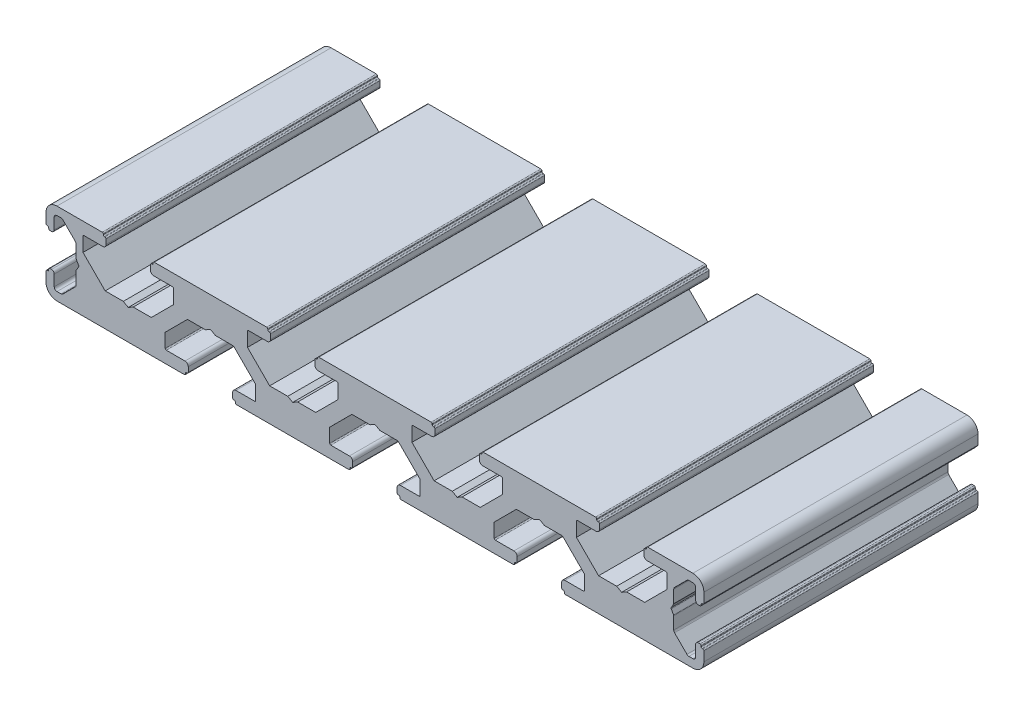
SolidWorks part; units mm, degrees
ref_plane "Płaszczyzna przednia" through (0, 0, 0) normal (0, 0, 1) x (1, 0, 0)
ref_plane "Płaszczyzna górna" through (0, 0, 0) normal (0, 1, 0) x (1, 0, 0)
ref_plane "Płaszczyzna prawa" through (0, 0, 0) normal (1, 0, 0) x (0, 0, -1)
sketch "Szkic1" plane through (0, 0, 0) normal (0, 0, 1) x (1, 0, 0)
  line L0 (141.56, 44.5751) -> (142.46, 44.06)
  line L1 (142.46, 44.06) -> (145.7645, 44.06)
  line L2 (145.7645, 44.06) -> (149.81, 40.01)
  line L3 (149.81, 40.01) -> (149.81, 37.46)
  line L4 (149.61, 37.26) -> (146.21, 37.26)
  line L5 (145.61, 36.66) -> (145.61, 35.76)
  line L6 (145.81, 35.56) -> (145.91, 35.56)
  line L7 (146.11, 35.36) -> (146.11, 35.26)
  line L8 (83.56, 50.06) -> (91.81, 50.06)
  line L9 (83.56, 35.06) -> (106.81, 35.06)
  line L10 (131.11, 49.86) -> (131.11, 49.76)
  line L11 (130.91, 49.56) -> (130.81, 49.56)
  line L12 (130.61, 49.36) -> (130.61, 48.46)
  line L13 (131.21, 47.86) -> (134.61, 47.86)
  line L14 (134.81, 47.66) -> (134.81, 45.11)
  line L15 (134.81, 45.11) -> (130.7645, 41.06)
  line L16 (130.7645, 41.06) -> (127.46, 41.06)
  line L17 (127.46, 41.06) -> (126.56, 40.5449)
  line L18 (126.56, 40.5449) -> (125.66, 41.06)
  line L19 (125.66, 41.06) -> (122.3555, 41.06)
  line L20 (122.3555, 41.06) -> (118.31, 45.11)
  line L21 (118.31, 45.11) -> (118.31, 47.66)
  line L22 (118.51, 47.86) -> (121.91, 47.86)
  line L23 (122.51, 48.46) -> (122.51, 49.36)
  line L24 (111.56, 44.5751) -> (112.46, 44.06)
  line L25 (112.46, 44.06) -> (115.7645, 44.06)
  line L26 (115.7645, 44.06) -> (119.81, 40.01)
  line L27 (119.81, 40.01) -> (119.81, 37.46)
  line L28 (119.61, 37.26) -> (116.21, 37.26)
  line L29 (115.61, 36.66) -> (115.61, 35.76)
  line L30 (115.81, 35.56) -> (115.91, 35.56)
  line L31 (116.11, 35.36) -> (116.11, 35.26)
  line L32 (101.31, 50.06) -> (121.81, 50.06)
  line L33 (122.31, 49.56) -> (122.21, 49.56)
  line L34 (122.01, 49.76) -> (122.01, 49.86)
  line L35 (116.31, 35.06) -> (136.81, 35.06)
  line L36 (131.31, 50.06) -> (151.81, 50.06)
  line L37 (137.01, 35.26) -> (137.01, 35.36)
  line L38 (137.21, 35.56) -> (137.31, 35.56)
  line L39 (137.51, 35.76) -> (137.51, 36.66)
  line L40 (136.91, 37.26) -> (133.51, 37.26)
  line L41 (133.31, 37.46) -> (133.31, 40.01)
  line L42 (133.31, 40.01) -> (137.3555, 44.06)
  line L43 (137.3555, 44.06) -> (140.66, 44.06)
  line L44 (140.66, 44.06) -> (141.56, 44.5751)
  line L45 (171.56, 44.5751) -> (172.46, 44.06)
  line L46 (172.46, 44.06) -> (175.7645, 44.06)
  line L47 (175.7645, 44.06) -> (179.81, 40.01)
  line L48 (179.81, 40.01) -> (179.81, 37.46)
  line L49 (179.61, 37.26) -> (176.21, 37.26)
  line L50 (175.61, 36.66) -> (175.61, 35.76)
  line L51 (146.31, 35.06) -> (166.81, 35.06)
  line L52 (101.11, 49.86) -> (101.11, 49.76)
  line L53 (100.91, 49.56) -> (100.81, 49.56)
  line L54 (100.61, 49.36) -> (100.61, 48.46)
  line L55 (101.21, 47.86) -> (104.61, 47.86)
  line L56 (104.81, 47.66) -> (104.81, 45.11)
  line L57 (104.81, 45.11) -> (100.7645, 41.06)
  line L58 (100.7645, 41.06) -> (97.46, 41.06)
  line L59 (97.46, 41.06) -> (96.56, 40.5449)
  line L60 (96.56, 40.5449) -> (95.66, 41.06)
  line L61 (95.66, 41.06) -> (92.3555, 41.06)
  line L62 (92.3555, 41.06) -> (88.31, 45.11)
  line L63 (88.31, 45.11) -> (88.31, 47.66)
  line L64 (88.51, 47.86) -> (91.91, 47.86)
  line L65 (92.51, 48.46) -> (92.51, 49.36)
  line L66 (92.31, 49.56) -> (92.21, 49.56)
  line L67 (92.01, 49.76) -> (92.01, 49.86)
  line L68 (161.31, 50.06) -> (181.81, 50.06)
  line L69 (175.81, 35.56) -> (175.91, 35.56)
  line L70 (176.11, 35.36) -> (176.11, 35.26)
  line L71 (176.31, 35.06) -> (199.56, 35.06)
  line L72 (191.31, 50.06) -> (199.56, 50.06)
  line L73 (161.11, 49.86) -> (161.11, 49.76)
  line L74 (160.91, 49.56) -> (160.81, 49.56)
  line L75 (160.61, 49.36) -> (160.61, 48.46)
  line L76 (161.21, 47.86) -> (164.61, 47.86)
  line L77 (164.81, 47.66) -> (164.81, 45.11)
  line L78 (164.81, 45.11) -> (160.7645, 41.06)
  line L79 (160.7645, 41.06) -> (157.46, 41.06)
  line L80 (157.46, 41.06) -> (156.56, 40.5449)
  line L81 (156.56, 40.5449) -> (155.66, 41.06)
  line L82 (155.66, 41.06) -> (152.3555, 41.06)
  line L83 (152.3555, 41.06) -> (148.31, 45.11)
  line L84 (148.31, 45.11) -> (148.31, 47.66)
  line L85 (148.51, 47.86) -> (151.91, 47.86)
  line L86 (152.51, 48.46) -> (152.51, 49.36)
  line L88 (107.01, 35.26) -> (107.01, 35.36)
  line L89 (107.21, 35.56) -> (107.31, 35.56)
  line L90 (107.51, 35.76) -> (107.51, 36.66)
  line L91 (106.91, 37.26) -> (103.51, 37.26)
  line L92 (103.31, 37.46) -> (103.31, 40.01)
  line L93 (103.31, 40.01) -> (107.3555, 44.06)
  line L94 (107.3555, 44.06) -> (110.66, 44.06)
  line L95 (110.66, 44.06) -> (111.56, 44.5751)
  line L96 (152.31, 49.56) -> (152.21, 49.56)
  line L97 (152.01, 49.76) -> (152.01, 49.86)
  line L100 (167.01, 35.26) -> (167.01, 35.36)
  line L101 (167.21, 35.56) -> (167.31, 35.56)
  line L102 (167.51, 35.76) -> (167.51, 36.66)
  line L103 (166.91, 37.26) -> (163.51, 37.26)
  line L104 (163.31, 37.46) -> (163.31, 40.01)
  line L105 (163.31, 40.01) -> (167.3555, 44.06)
  line L106 (167.3555, 44.06) -> (170.66, 44.06)
  line L107 (170.66, 44.06) -> (171.56, 44.5751)
  line L118 (191.11, 49.86) -> (191.11, 49.76)
  line L119 (190.91, 49.56) -> (190.81, 49.56)
  line L120 (190.61, 49.36) -> (190.61, 48.46)
  line L121 (191.21, 47.86) -> (194.61, 47.86)
  line L122 (194.81, 47.66) -> (194.81, 45.11)
  line L123 (194.81, 45.11) -> (190.7645, 41.06)
  line L124 (190.7645, 41.06) -> (187.46, 41.06)
  line L125 (187.46, 41.06) -> (186.56, 40.5449)
  line L126 (186.56, 40.5449) -> (185.66, 41.06)
  line L127 (185.66, 41.06) -> (182.3555, 41.06)
  line L128 (182.3555, 41.06) -> (178.31, 45.11)
  line L129 (178.31, 45.11) -> (178.31, 47.66)
  line L130 (178.51, 47.86) -> (181.91, 47.86)
  line L131 (182.51, 48.46) -> (182.51, 49.36)
  line L132 (182.31, 49.56) -> (182.21, 49.56)
  line L133 (182.01, 49.76) -> (182.01, 49.86)
  line L144 (201.56, 44.5751) -> (202.46, 44.06) [skipped]
  line L145 (202.46, 44.06) -> (205.7645, 44.06) [skipped]
  line L146 (205.7645, 44.06) -> (209.81, 40.01) [skipped]
  line L147 (209.81, 40.01) -> (209.81, 37.46) [skipped]
  line L148 (209.61, 37.26) -> (206.21, 37.26) [skipped]
  line L149 (205.61, 36.66) -> (205.61, 35.76) [skipped]
  line L150 (205.81, 35.56) -> (205.91, 35.56) [skipped]
  line L151 (206.11, 35.36) -> (206.11, 35.26) [skipped]
  line L152 (206.31, 35.06) -> (214.56, 35.06) [skipped]
  line L153 (188.56, 35.06) -> (196.81, 35.06) [skipped]
  line L154 (197.01, 35.26) -> (197.01, 35.36) [skipped]
  line L155 (197.21, 35.56) -> (197.31, 35.56) [skipped]
  line L156 (197.51, 35.76) -> (197.51, 36.66) [skipped]
  line L157 (196.91, 37.26) -> (193.51, 37.26) [skipped]
  line L158 (193.31, 40.01) -> (197.3555, 44.06) [skipped]
  line L159 (197.3555, 44.06) -> (200.66, 44.06) [skipped]
  line L160 (200.66, 44.06) -> (201.56, 44.5751) [skipped]
  line L161 (193.31, 37.46) -> (193.31, 40.01) [skipped]
  line L176 (201.56, 46.31) -> (201.56, 48.06)
  line L177 (201.26, 46.11) -> (201.36, 46.11)
  line L178 (201.06, 45.76) -> (201.06, 45.91)
  line L179 (200.56, 45.56) -> (200.86, 45.56)
  line L180 (200.06, 48.06) -> (200.06, 46.06)
  line L181 (198.8278, 48.56) -> (199.56, 48.56)
  line L182 (196.2064, 46.1458) -> (198.4742, 48.4136)
  line L183 (196.06, 43.5136) -> (196.06, 45.7922)
  line L184 (195.5981, 42.66) -> (196.0332, 43.4136)
  line L185 (196.0332, 41.7064) -> (195.5981, 42.46)
  line L186 (196.06, 39.3278) -> (196.06, 41.6064)
  line L187 (198.4742, 36.7064) -> (196.2064, 38.9742)
  line L188 (199.56, 36.56) -> (198.8278, 36.56)
  line L189 (200.06, 39.06) -> (200.06, 37.06)
  line L190 (200.86, 39.56) -> (200.56, 39.56)
  line L191 (201.06, 39.21) -> (201.06, 39.36)
  line L192 (201.36, 39.01) -> (201.26, 39.01)
  line L193 (201.56, 37.06) -> (201.56, 38.81)
  line L212 (81.56, 38.81) -> (81.56, 37.06)
  line L213 (81.86, 39.01) -> (81.76, 39.01)
  line L214 (82.06, 39.36) -> (82.06, 39.21)
  line L215 (82.56, 39.56) -> (82.26, 39.56)
  line L216 (83.06, 37.06) -> (83.06, 39.06)
  line L217 (84.2922, 36.56) -> (83.56, 36.56)
  line L218 (86.9136, 38.9742) -> (84.6458, 36.7064)
  line L219 (87.06, 41.6064) -> (87.06, 39.3278)
  line L220 (87.5219, 42.46) -> (87.0868, 41.7064)
  line L221 (87.0868, 43.4136) -> (87.5219, 42.66)
  line L222 (87.06, 45.7922) -> (87.06, 43.5136)
  line L223 (84.6458, 48.4136) -> (86.9136, 46.1458)
  line L224 (83.56, 48.56) -> (84.2922, 48.56)
  line L225 (83.06, 46.06) -> (83.06, 48.06)
  line L226 (82.26, 45.56) -> (82.56, 45.56)
  line L227 (82.06, 45.91) -> (82.06, 45.76)
  line L228 (81.76, 46.11) -> (81.86, 46.11)
  line L229 (81.56, 48.06) -> (81.56, 46.31)
  line L230 (91.81, 50.06) -> (83.56, 50.06) [skipped]
  line L231 (199.56, 50.06) -> (191.31, 50.06) [skipped]
  line L232 (98.56, 35.06) -> (106.81, 35.06) [skipped]
  line L233 (109.56, 50.06) -> (101.31, 50.06) [skipped]
  line L234 (121.81, 50.06) -> (113.56, 50.06) [skipped]
  line L235 (116.31, 35.06) -> (124.56, 35.06) [skipped]
  line L236 (128.56, 35.06) -> (136.81, 35.06) [skipped]
  line L237 (139.56, 50.06) -> (131.31, 50.06) [skipped]
  line L238 (151.81, 50.06) -> (143.56, 50.06) [skipped]
  line L239 (146.31, 35.06) -> (154.56, 35.06) [skipped]
  line L240 (158.56, 35.06) -> (166.81, 35.06) [skipped]
  line L241 (169.56, 50.06) -> (161.31, 50.06) [skipped]
  line L242 (181.81, 50.06) -> (173.56, 50.06) [skipped]
  line L243 (176.31, 35.06) -> (184.56, 35.06) [skipped]
  arc A0 (149.61, 37.26) -> (149.81, 37.46) centre (149.61, 37.46) ccw
  arc A1 (146.21, 37.26) -> (145.61, 36.66) centre (146.21, 36.66) ccw
  arc A2 (145.61, 35.76) -> (145.81, 35.56) centre (145.81, 35.76) ccw
  arc A3 (146.11, 35.36) -> (145.91, 35.56) centre (145.91, 35.36) ccw
  arc A4 (146.11, 35.26) -> (146.31, 35.06) centre (146.31, 35.26) ccw
  arc A5 (131.31, 50.06) -> (131.11, 49.86) centre (131.31, 49.86) ccw
  arc A6 (130.91, 49.56) -> (131.11, 49.76) centre (130.91, 49.76) ccw
  arc A7 (130.81, 49.56) -> (130.61, 49.36) centre (130.81, 49.36) ccw
  arc A8 (130.61, 48.46) -> (131.21, 47.86) centre (131.21, 48.46) ccw
  arc A9 (134.81, 47.66) -> (134.61, 47.86) centre (134.61, 47.66) ccw
  arc A10 (118.51, 47.86) -> (118.31, 47.66) centre (118.51, 47.66) ccw
  arc A11 (121.91, 47.86) -> (122.51, 48.46) centre (121.91, 48.46) ccw
  arc A12 (122.51, 49.36) -> (122.31, 49.56) centre (122.31, 49.36) ccw
  arc A13 (122.01, 49.76) -> (122.21, 49.56) centre (122.21, 49.76) ccw
  arc A14 (122.01, 49.86) -> (121.81, 50.06) centre (121.81, 49.86) ccw
  arc A15 (136.81, 35.06) -> (137.01, 35.26) centre (136.81, 35.26) ccw
  arc A16 (137.21, 35.56) -> (137.01, 35.36) centre (137.21, 35.36) ccw
  arc A17 (137.31, 35.56) -> (137.51, 35.76) centre (137.31, 35.76) ccw
  arc A18 (137.51, 36.66) -> (136.91, 37.26) centre (136.91, 36.66) ccw
  arc A19 (133.31, 37.46) -> (133.51, 37.26) centre (133.51, 37.46) ccw
  arc A20 (179.61, 37.26) -> (179.81, 37.46) centre (179.61, 37.46) ccw
  arc A21 (176.21, 37.26) -> (175.61, 36.66) centre (176.21, 36.66) ccw
  arc A22 (175.61, 35.76) -> (175.81, 35.56) centre (175.81, 35.76) ccw
  arc A23 (176.11, 35.36) -> (175.91, 35.56) centre (175.91, 35.36) ccw
  arc A24 (119.61, 37.26) -> (119.81, 37.46) centre (119.61, 37.46) ccw
  arc A25 (116.21, 37.26) -> (115.61, 36.66) centre (116.21, 36.66) ccw
  arc A26 (115.61, 35.76) -> (115.81, 35.56) centre (115.81, 35.76) ccw
  arc A27 (116.11, 35.36) -> (115.91, 35.56) centre (115.91, 35.36) ccw
  arc A28 (116.11, 35.26) -> (116.31, 35.06) centre (116.31, 35.26) ccw
  arc A29 (176.11, 35.26) -> (176.31, 35.06) centre (176.31, 35.26) ccw
  arc A30 (161.31, 50.06) -> (161.11, 49.86) centre (161.31, 49.86) ccw
  arc A31 (160.91, 49.56) -> (161.11, 49.76) centre (160.91, 49.76) ccw
  arc A32 (160.81, 49.56) -> (160.61, 49.36) centre (160.81, 49.36) ccw
  arc A33 (160.61, 48.46) -> (161.21, 47.86) centre (161.21, 48.46) ccw
  arc A34 (164.81, 47.66) -> (164.61, 47.86) centre (164.61, 47.66) ccw
  arc A35 (148.51, 47.86) -> (148.31, 47.66) centre (148.51, 47.66) ccw
  arc A36 (151.91, 47.86) -> (152.51, 48.46) centre (151.91, 48.46) ccw
  arc A37 (152.51, 49.36) -> (152.31, 49.56) centre (152.31, 49.36) ccw
  arc A38 (152.01, 49.76) -> (152.21, 49.56) centre (152.21, 49.76) ccw
  arc A39 (152.01, 49.86) -> (151.81, 50.06) centre (151.81, 49.86) ccw
  arc A40 (166.81, 35.06) -> (167.01, 35.26) centre (166.81, 35.26) ccw
  arc A41 (101.31, 50.06) -> (101.11, 49.86) centre (101.31, 49.86) ccw
  arc A42 (100.91, 49.56) -> (101.11, 49.76) centre (100.91, 49.76) ccw
  arc A43 (100.81, 49.56) -> (100.61, 49.36) centre (100.81, 49.36) ccw
  arc A44 (100.61, 48.46) -> (101.21, 47.86) centre (101.21, 48.46) ccw
  arc A45 (104.81, 47.66) -> (104.61, 47.86) centre (104.61, 47.66) ccw
  arc A46 (88.51, 47.86) -> (88.31, 47.66) centre (88.51, 47.66) ccw
  arc A47 (91.91, 47.86) -> (92.51, 48.46) centre (91.91, 48.46) ccw
  arc A48 (92.51, 49.36) -> (92.31, 49.56) centre (92.31, 49.36) ccw
  arc A49 (92.01, 49.76) -> (92.21, 49.56) centre (92.21, 49.76) ccw
  arc A50 (92.01, 49.86) -> (91.81, 50.06) centre (91.81, 49.86) ccw
  arc A51 (167.21, 35.56) -> (167.01, 35.36) centre (167.21, 35.36) ccw
  arc A52 (167.31, 35.56) -> (167.51, 35.76) centre (167.31, 35.76) ccw
  arc A53 (167.51, 36.66) -> (166.91, 37.26) centre (166.91, 36.66) ccw
  arc A54 (163.31, 37.46) -> (163.51, 37.26) centre (163.51, 37.46) ccw
  arc A55 (83.56, 50.06) -> (81.56, 48.06) centre (83.56, 48.06) ccw
  arc A56 (83.56, 35.06) -> (81.56, 37.06) centre (83.56, 37.06) cw
  arc A57 (201.56, 37.06) -> (199.56, 35.06) centre (199.56, 37.06) cw
  arc A58 (199.56, 50.06) -> (201.56, 48.06) centre (199.56, 48.06) cw
  arc A60 (191.31, 50.06) -> (191.11, 49.86) centre (191.31, 49.86) ccw
  arc A61 (190.91, 49.56) -> (191.11, 49.76) centre (190.91, 49.76) ccw
  arc A62 (190.81, 49.56) -> (190.61, 49.36) centre (190.81, 49.36) ccw
  arc A63 (106.81, 35.06) -> (107.01, 35.26) centre (106.81, 35.26) ccw
  arc A64 (107.21, 35.56) -> (107.01, 35.36) centre (107.21, 35.36) ccw
  arc A65 (107.31, 35.56) -> (107.51, 35.76) centre (107.31, 35.76) ccw
  arc A66 (107.51, 36.66) -> (106.91, 37.26) centre (106.91, 36.66) ccw
  arc A67 (103.31, 37.46) -> (103.51, 37.26) centre (103.51, 37.46) ccw
  arc A68 (190.61, 48.46) -> (191.21, 47.86) centre (191.21, 48.46) ccw
  arc A69 (194.81, 47.66) -> (194.61, 47.86) centre (194.61, 47.66) ccw
  arc A70 (178.51, 47.86) -> (178.31, 47.66) centre (178.51, 47.66) ccw
  arc A71 (181.91, 47.86) -> (182.51, 48.46) centre (181.91, 48.46) ccw
  arc A72 (182.51, 49.36) -> (182.31, 49.56) centre (182.31, 49.36) ccw
  arc A73 (182.01, 49.76) -> (182.21, 49.56) centre (182.21, 49.76) ccw
  arc A74 (182.01, 49.86) -> (181.81, 50.06) centre (181.81, 49.86) ccw
  arc A80 (209.61, 37.26) -> (209.81, 37.46) centre (209.61, 37.46) ccw [skipped]
  arc A81 (206.21, 37.26) -> (205.61, 36.66) centre (206.21, 36.66) ccw [skipped]
  arc A82 (205.61, 35.76) -> (205.81, 35.56) centre (205.81, 35.76) ccw [skipped]
  arc A83 (206.11, 35.36) -> (205.91, 35.56) centre (205.91, 35.36) ccw [skipped]
  arc A84 (206.11, 35.26) -> (206.31, 35.06) centre (206.31, 35.26) ccw [skipped]
  arc A85 (196.81, 35.06) -> (197.01, 35.26) centre (196.81, 35.26) ccw [skipped]
  arc A86 (197.21, 35.56) -> (197.01, 35.36) centre (197.21, 35.36) ccw [skipped]
  arc A87 (197.31, 35.56) -> (197.51, 35.76) centre (197.31, 35.76) ccw [skipped]
  arc A88 (197.51, 36.66) -> (196.91, 37.26) centre (196.91, 36.66) ccw [skipped]
  arc A89 (193.31, 37.46) -> (193.51, 37.26) centre (193.51, 37.46) ccw [skipped]
  arc A106 (201.36, 46.11) -> (201.56, 46.31) centre (201.36, 46.31) ccw
  arc A107 (201.26, 46.11) -> (201.06, 45.91) centre (201.26, 45.91) ccw
  arc A108 (200.86, 45.56) -> (201.06, 45.76) centre (200.86, 45.76) ccw
  arc A109 (200.06, 46.06) -> (200.56, 45.56) centre (200.56, 46.06) ccw
  arc A110 (200.06, 48.06) -> (199.56, 48.56) centre (199.56, 48.06) ccw
  arc A111 (198.8278, 48.56) -> (198.4742, 48.4136) centre (198.8278, 48.06) ccw
  arc A112 (196.2064, 46.1458) -> (196.06, 45.7922) centre (196.56, 45.7922) ccw
  arc A113 (196.0332, 43.4136) -> (196.06, 43.5136) centre (195.86, 43.5136) ccw
  arc A114 (195.5981, 42.66) -> (195.5981, 42.46) centre (195.7713, 42.56) ccw
  arc A115 (196.06, 41.6064) -> (196.0332, 41.7064) centre (195.86, 41.6064) ccw
  arc A116 (196.06, 39.3278) -> (196.2064, 38.9742) centre (196.56, 39.3278) ccw
  arc A117 (198.4742, 36.7064) -> (198.8278, 36.56) centre (198.8278, 37.06) ccw
  arc A118 (199.56, 36.56) -> (200.06, 37.06) centre (199.56, 37.06) ccw
  arc A119 (200.56, 39.56) -> (200.06, 39.06) centre (200.56, 39.06) ccw
  arc A120 (201.06, 39.36) -> (200.86, 39.56) centre (200.86, 39.36) ccw
  arc A121 (201.06, 39.21) -> (201.26, 39.01) centre (201.26, 39.21) ccw
  arc A122 (201.56, 38.81) -> (201.36, 39.01) centre (201.36, 38.81) ccw
  arc A142 (81.76, 39.01) -> (81.56, 38.81) centre (81.76, 38.81) ccw
  arc A143 (81.86, 39.01) -> (82.06, 39.21) centre (81.86, 39.21) ccw
  arc A144 (82.26, 39.56) -> (82.06, 39.36) centre (82.26, 39.36) ccw
  arc A145 (83.06, 39.06) -> (82.56, 39.56) centre (82.56, 39.06) ccw
  arc A146 (83.06, 37.06) -> (83.56, 36.56) centre (83.56, 37.06) ccw
  arc A147 (84.2922, 36.56) -> (84.6458, 36.7064) centre (84.2922, 37.06) ccw
  arc A148 (86.9136, 38.9742) -> (87.06, 39.3278) centre (86.56, 39.3278) ccw
  arc A149 (87.0868, 41.7064) -> (87.06, 41.6064) centre (87.26, 41.6064) ccw
  arc A150 (87.5219, 42.46) -> (87.5219, 42.66) centre (87.3487, 42.56) ccw
  arc A151 (87.06, 43.5136) -> (87.0868, 43.4136) centre (87.26, 43.5136) ccw
  arc A152 (87.06, 45.7922) -> (86.9136, 46.1458) centre (86.56, 45.7922) ccw
  arc A153 (84.6458, 48.4136) -> (84.2922, 48.56) centre (84.2922, 48.06) ccw
  arc A154 (83.56, 48.56) -> (83.06, 48.06) centre (83.56, 48.06) ccw
  arc A155 (82.56, 45.56) -> (83.06, 46.06) centre (82.56, 46.06) ccw
  arc A156 (82.06, 45.76) -> (82.26, 45.56) centre (82.26, 45.76) ccw
  arc A157 (82.06, 45.91) -> (81.86, 46.11) centre (81.86, 45.91) ccw
  arc A158 (81.56, 46.31) -> (81.76, 46.11) centre (81.76, 46.31) ccw
  dimension "D1" = 4
  dimension "D2" = 2
extrude "Dodanie-wyciągnięcie1" add sketch "Szkic1" along normal blind 50
